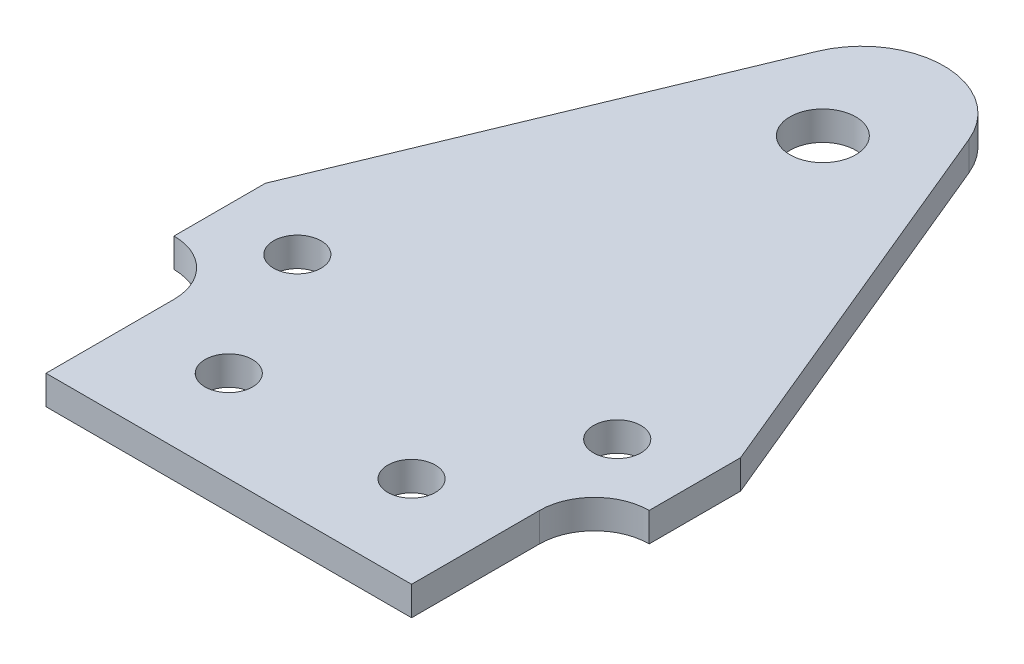
SolidWorks part; units mm, degrees
material "6061-T6 (SS)"
ref_plane "Front Plane" through (0, 0, 0) normal (0, 0, 1) x (1, 0, 0)
ref_plane "Top Plane" through (0, 0, 0) normal (0, 1, 0) x (1, 0, 0)
ref_plane "Right Plane" through (0, 0, 0) normal (1, 0, 0) x (0, 0, -1)
sketch "Sketch1" plane through (0, 0, 0) normal (0, 1, 0) x (1, 0, 0)
  line L0 (8.3149, 72.6956) -> (26, 30)
  line L1 (0, 0) -> (0, 78.2515) construction
  line L2 (26, 30) -> (26, 20)
  line L3 (20, 0) -> (20, 14)
  line L96 (20, 0) -> (-20, 0)
  line L97 (-20, 0) -> (-20, 14)
  line L98 (-26, 30) -> (-26, 20)
  line L99 (-8.3149, 72.6956) -> (-26, 30)
  arc A0 (-20, 14) -> (-26, 20) centre (-26, 14) ccw
  circle A1 centre (10, 10) radius 2.6
  circle A2 centre (-17.5, 25) radius 2.6
  circle A3 centre (0, 65) radius 3.6
  circle A4 centre (17.5, 25) radius 2.6
  circle A5 centre (-10, 10) radius 2.6
  arc A6 (20, 14) -> (26, 20) centre (26, 14) cw
  arc A7 (-8.3149, 72.6956) -> (8.3149, 72.6956) centre (0, 69.2515) cw
  point P2 (0, 78.2515)
  dimension "D4" = 6
  dimension "D5" = 10
  dimension "D6" = 10
  dimension "D7" = 25
  dimension "D8" = 35
  dimension "D10" = 40
  dimension "D11" = 9
  dimension "D12" = 5.2
  dimension "D13" = 7.2
  dimension "D1" = 40
  dimension "D2" = 52
  dimension "D3" = 14
  dimension "D9" = 22.5
  dimension "D14" = 10
extrude "Boss-Extrude1" add sketch "Sketch1" along normal blind 3.175
